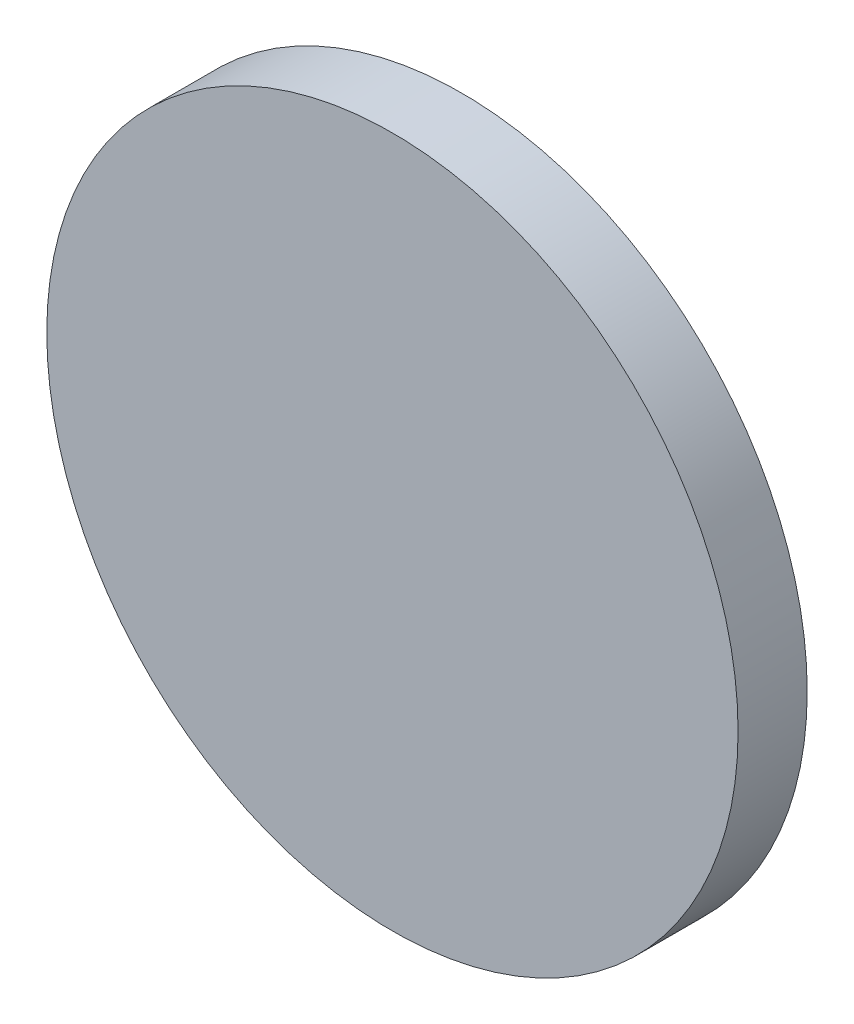
SolidWorks part; units mm, degrees
ref_plane "前视基准面" through (0, 0, 0) normal (0, 0, 1) x (1, 0, 0)
ref_plane "上视基准面" through (0, 0, 0) normal (0, 1, 0) x (1, 0, 0)
ref_plane "右视基准面" through (0, 0, 0) normal (1, 0, 0) x (0, 0, -1)
sketch "草图1" plane through (0, 0, 0) normal (0, 0, 1) x (1, 0, 0)
  circle A0 centre (0, 0) radius 15
  dimension "D1" = 30
extrude "凸台-拉伸1" add sketch "草图1" along normal blind 3 contours A0
